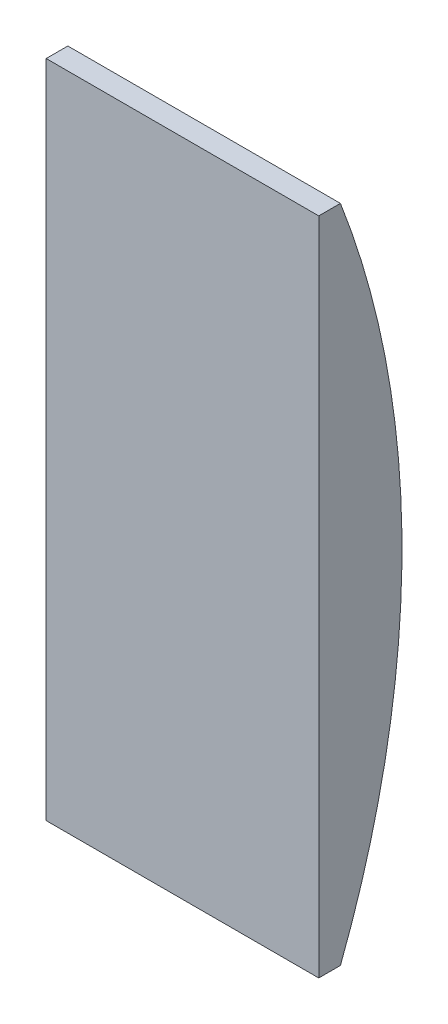
SolidWorks part; units mm, degrees
ref_plane "Front Plane" through (0, 0, 0) normal (0, 0, 1) x (1, 0, 0)
ref_plane "Top Plane" through (0, 0, 0) normal (0, 1, 0) x (1, 0, 0)
ref_plane "Right Plane" through (0, 0, 0) normal (1, 0, 0) x (0, 0, -1)
sketch "Sketch1" plane through (0, 0, 0) normal (1, 0, 0) x (0, 0, -1)
  line L0 (0, 94.869) -> (3.114, 94.869)
  line L1 (0, 0) -> (3.114, 0)
  line L2 (0, 0) -> (0, 94.869)
  line L3 (0, 47.4345) -> (11.9609, 47.4345) construction
  arc A0 (3.114, 94.869) -> (3.114, 0) centre (-119.6287, 47.4345) cw
  dimension "D1" = 3.114
  dimension "D2" = 3.114
  dimension "D3" = 94.869
  dimension "D4" = 11.9609
extrude "Boss-Extrude1" add sketch "Sketch1" along normal blind 39.1795
